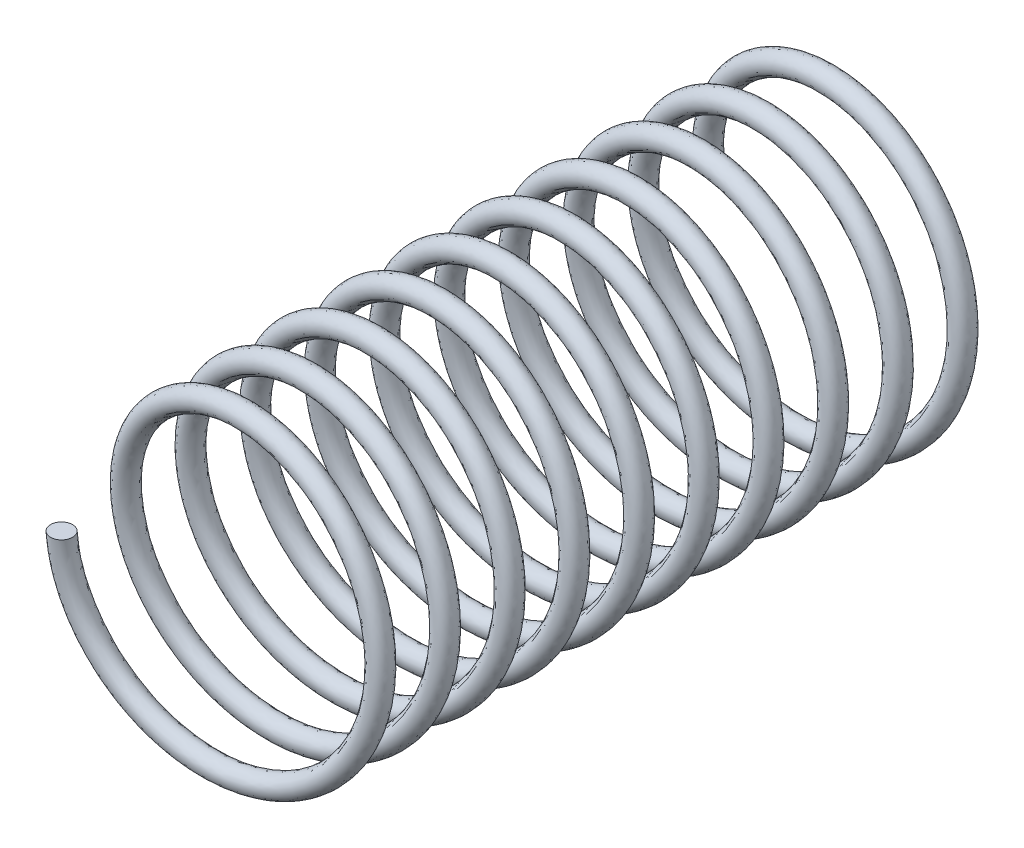
SolidWorks part; units mm, degrees
ref_plane "Front Plane" through (0, 0, 0) normal (0, 0, 1) x (1, 0, 0)
ref_plane "Top Plane" through (0, 0, 0) normal (0, 1, 0) x (1, 0, 0)
ref_plane "Right Plane" through (0, 0, 0) normal (1, 0, 0) x (0, 0, -1)
sketch "Sketch1" plane through (0, 0, 0) normal (0, 0, 1) x (1, 0, 0)
  circle A0 centre (0, 0) radius 14
sketch "Sketch3" plane through (0, 0, 0) normal (0, 0, 1) x (1, 0, 0)
  circle A0 centre (13, 0) radius 13
  point P4 (8.2777, 0)
curve "Helix/Spiral2" pitch 5.88 height 58.8 turns 10
sketch "Sketch4" plane through (0, 0, 0) normal (0, 1, 0) x (1, 0, 0)
  circle A0 centre (0, 0) radius 1
sweep "Sweep1" add profiles "Sketch4" path "Helix/Spiral2"
